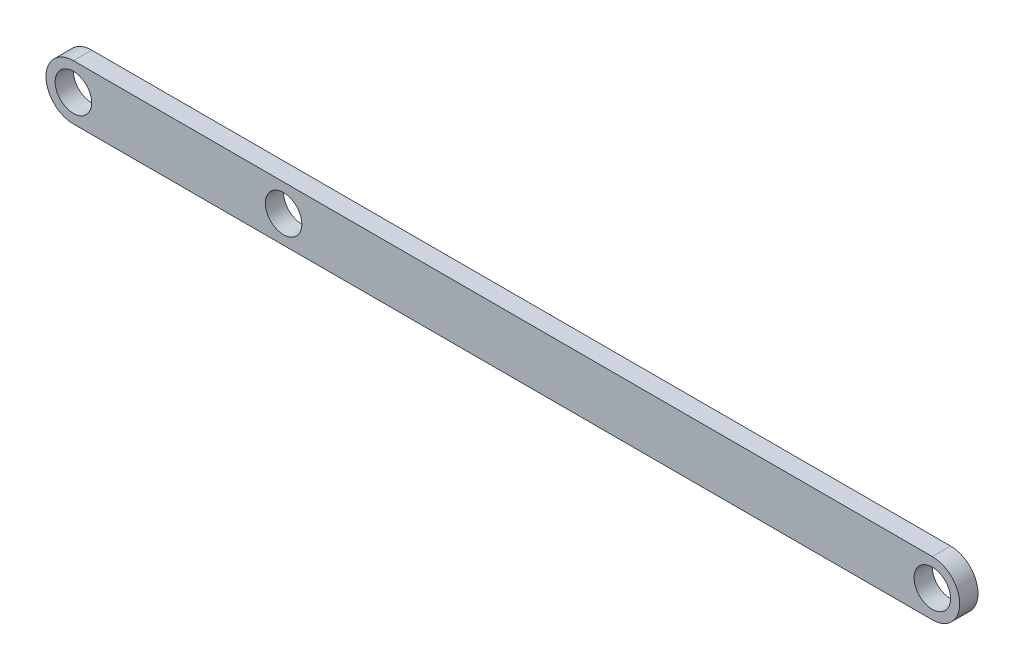
SolidWorks part; units mm, degrees
ref_plane "Front Plane" through (0, 0, 0) normal (0, 0, 1) x (1, 0, 0)
ref_plane "Top Plane" through (0, 0, 0) normal (0, 1, 0) x (1, 0, 0)
ref_plane "Right Plane" through (0, 0, 0) normal (1, 0, 0) x (0, 0, -1)
other "Center of Mass"
sketch "Sketch3" plane through (0, 0, 0) normal (0, 0, 1) x (1, 0, 0)
  line L0 (-250, 0) -> (0, 0)
  line L1 (-250, 0) -> (-250, 15)
  line L2 (-250, 15) -> (0, 15)
  line L3 (0, 15) -> (0, 0)
  dimension "D1" = 15
  dimension "D2" = 250
extrude "Boss-Extrude4" add sketch "Sketch3" along normal blind 5
sketch "Sketch7" plane through (0, 0, 5) normal (0, 0, 1) x (1, 0, 0)
  line L0 (-250, 7.5) -> (0, 7.5) construction
  line L1 (-250, 15) -> (-250, 0) construction
  line L2 (0, 0) -> (0, 15) construction
  line L3 (-125, 15) -> (-125, 0) construction
  line L7 (-250, 15) -> (-250, 0)
  line L8 (-250, 0) -> (0, 0)
  line L9 (0, 0) -> (0, 15)
  line L10 (0, 15) -> (-250, 15)
  line L11 (-250, 15) -> (-250, 0)
  line L12 (-250, 0) -> (0, 0)
  line L13 (0, 0) -> (0, 15)
  line L14 (0, 15) -> (-250, 15)
  circle A0 centre (-242.5, 7.5) radius 7.5
  circle A1 centre (-242.5, 7.5) radius 5
  circle A2 centre (-7.5, 7.5) radius 5
  circle A3 centre (-7.5, 7.5) radius 7.5
  line M1 (-250, 15) -> (-250, 0)
  line M2 (-250, 0) -> (0, 0)
  line M3 (0, 0) -> (0, 15)
  line M4 (0, 15) -> (-250, 15)
  dimension "D1" = 15
  dimension "D3" = 0
  dimension "D2" = 7.5
extrude "Cut-Extrude3" cut sketch "Sketch7" against normal blind 5 contours A0 L14 M1 | A1 | A0 L11 M2 | A3 M3 M2 | A3 L13 M4 | A2
sketch "Sketch8" plane through (0, 0, 5) normal (0, 0, 1) x (1, 0, 0)
  line L0 (-250, 7.5) -> (1.4788, 7.5) construction
  arc A0 (-242.5, 15) -> (-242.5, 0) centre (-242.5, 7.5) ccw construction
  circle A1 centre (-185, 7.5) radius 5
  dimension "D1" = 65
extrude "Cut-Extrude5" cut sketch "Sketch8" against normal through all
